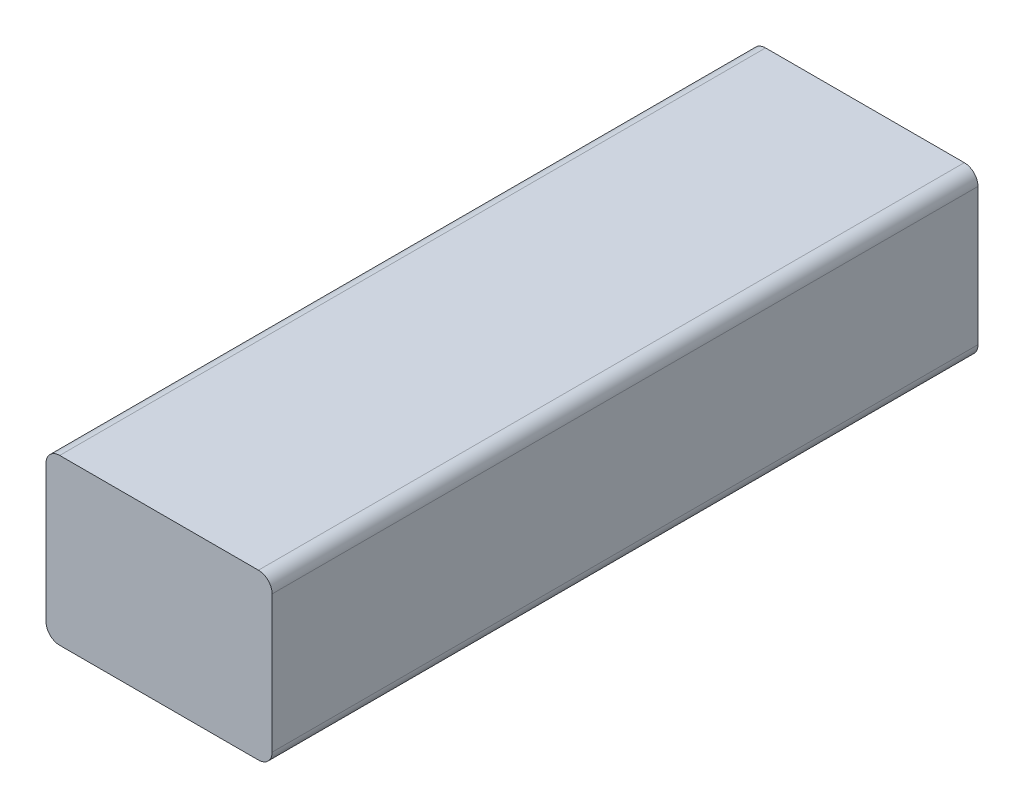
SolidWorks part; units mm, degrees
ref_plane "Front Plane" through (0, 0, 0) normal (0, 0, 1) x (1, 0, 0)
ref_plane "Top Plane" through (0, 0, 0) normal (0, 1, 0) x (1, 0, 0)
ref_plane "Right Plane" through (0, 0, 0) normal (1, 0, 0) x (0, 0, -1)
sketch "Sketch1" plane through (0, 0, 0) normal (0, 1, 0) x (1, 0, 0)
  line L1 (-16.5, -51.5) -> (16.5, -51.5)
  line L2 (-16.5, -51.5) -> (-16.5, 51.5)
  line L3 (-16.5, 51.5) -> (16.5, 51.5)
  line L4 (16.5, -51.5) -> (16.5, 51.5)
  line L5 (-16.5, -51.5) -> (16.5, 51.5) construction
  line L6 (-16.5, 51.5) -> (16.5, -51.5) construction
  point P0 (0, 0)
  dimension "D1" = 103
  dimension "D2" = 33
extrude "Boss-Extrude1" add sketch "Sketch1" along normal blind 24
fillet "Fillet1" radius 2 4 edges at (-16.5, 0, 0) (-16.5, 24, 0) (16.5, 0, 0) (16.5, 24, 0)
ref_plane "Plane1" through (0, 0, 0) normal (-1, 0, 0) x (0, 0, 1)
